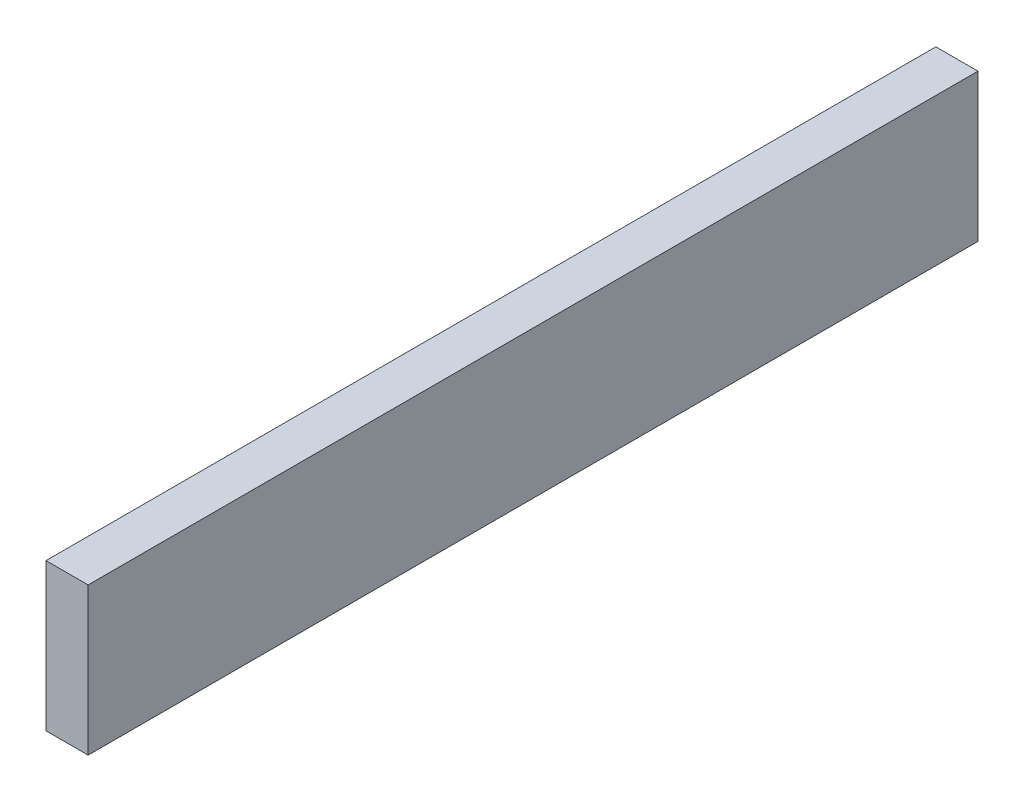
SolidWorks part; units mm, degrees
ref_plane "Front Plane" through (0, 0, 0) normal (0, 0, 1) x (1, 0, 0)
ref_plane "Top Plane" through (0, 0, 0) normal (0, 1, 0) x (1, 0, 0)
ref_plane "Right Plane" through (0, 0, 0) normal (1, 0, 0) x (0, 0, -1)
sketch "Sketch1" plane through (0, 0, 0) normal (1, 0, 0) x (0, 0, -1)
  line L1 (-42.25, 7) -> (42.25, 7)
  line L2 (-42.25, 7) -> (-42.25, -7)
  line L3 (-42.25, -7) -> (42.25, -7)
  line L4 (42.25, 7) -> (42.25, -7)
  line L5 (-42.25, 7) -> (42.25, -7) construction
  line L6 (-42.25, -7) -> (42.25, 7) construction
  point P0 (0, 0)
  dimension "D1" = 84.5
  dimension "D2" = 14
extrude "Boss-Extrude1" add sketch "Sketch1" against normal blind 4
